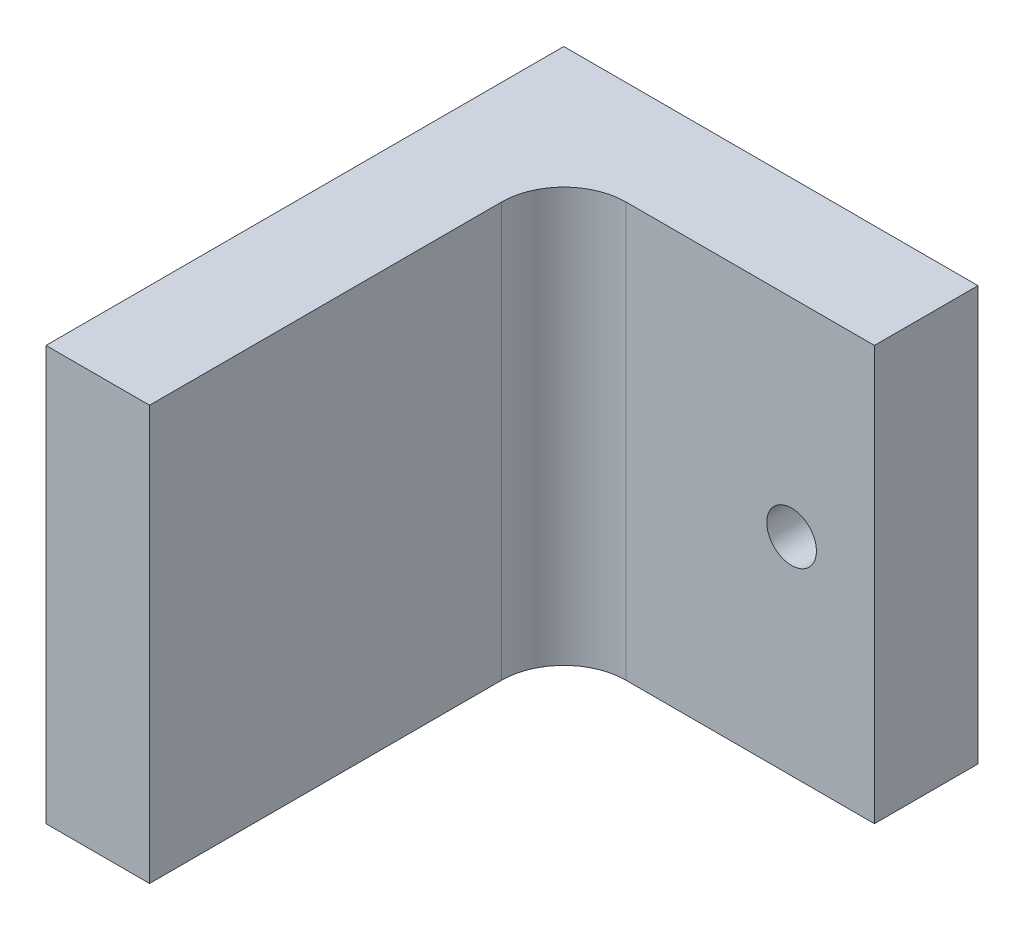
SolidWorks part; units mm, degrees
ref_plane "Front Plane" through (0, 0, 0) normal (0, 0, 1) x (1, 0, 0)
ref_plane "Top Plane" through (0, 0, 0) normal (0, 1, 0) x (1, 0, 0)
ref_plane "Right Plane" through (0, 0, 0) normal (1, 0, 0) x (0, 0, -1)
sketch "Sketch1" plane through (0, 0, 0) normal (0, 0, 1) x (1, 0, 0)
  line L1 (0, 0) -> (20, 0)
  line L2 (0, 0) -> (0, 20)
  line L3 (0, 20) -> (20, 20)
  line L4 (20, 0) -> (20, 20)
  dimension "D1" = 20
  dimension "20mm" = 20
extrude "Boss-Extrude1" add sketch "Sketch1" along normal blind 5
sketch "Sketch2" plane through (0, 0, 5) normal (0, 0, 1) x (1, 0, 0)
  line L0 (0, 0) -> (20, 0) construction
  line L1 (0, 20) -> (5, 20)
  line L2 (0, 20) -> (0, 0)
  line L3 (0, 0) -> (5, 0)
  line L4 (5, 20) -> (5, 0)
  dimension "D1" = 5
extrude "Boss-Extrude2" add sketch "Sketch2" along normal blind 20
fillet "Fillet1" radius 3 1 edges at (5, 10, 5)
sketch "Sketch3" plane through (0, 0, 0) normal (0, 0, -1) x (-1, 0, 0)
  line L0 (-16, 0) -> (-16, 20) construction
  line L1 (0, 0) -> (-20, 0) construction
  line L2 (-20, 20) -> (0, 20) construction
  circle A0 centre (-16, 10) radius 1.2
  dimension "D1" = 4
extrude "Cut-Extrude1" cut sketch "Sketch3" against normal blind 20
